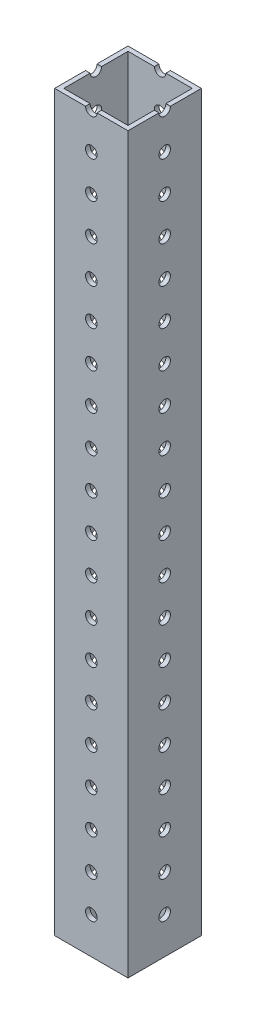
SolidWorks part; units mm, degrees
material "6061-T6 (SS)"
ref_plane "Front Plane" through (0, 0, 0) normal (0, 0, 1) x (1, 0, 0)
ref_plane "Top Plane" through (0, 0, 0) normal (0, 1, 0) x (1, 0, 0)
ref_plane "Right Plane" through (0, 0, 0) normal (1, 0, 0) x (0, 0, -1)
sketch "Sketch1" plane through (0, 0, 0) normal (0, 1, 0) x (1, 0, 0)
  line L0 (-11.1125, -11.1125) -> (-11.1125, 11.1125)
  line L1 (-12.7, -12.7) -> (12.7, -12.7)
  line L2 (-12.7, -12.7) -> (-12.7, 12.7)
  line L3 (-12.7, 12.7) -> (12.7, 12.7)
  line L4 (12.7, -12.7) -> (12.7, 12.7)
  line L5 (-12.7, -12.7) -> (12.7, 12.7) construction
  line L6 (-12.7, 12.7) -> (12.7, -12.7) construction
  line L7 (-11.1125, 11.1125) -> (11.1125, 11.1125)
  line L8 (11.1125, -11.1125) -> (11.1125, 11.1125)
  line L9 (-11.1125, -11.1125) -> (11.1125, -11.1125)
  point P0 (0, 0)
  dimension "D1" = 25.4
  dimension "D2" = 25.4
  dimension "D3" = 1.5875
extrude "Boss-Extrude1" add sketch "Sketch1" along normal blind 254
hole_wizard "#22 (0.157) Diameter Hole1" positions "Sketch2" profile "Sketch3" hole size "#22" standard "ANSI Inch" end condition through all
sketch "Sketch2" plane through (0, 0, 12.7) normal (0, 0, 1) x (1, 0, 0)
  line L0 (12.7, 254) -> (12.7, 0) construction
  line L1 (-12.7, 0) -> (12.7, 0) construction
  point P0 (0, 12.7)
  dimension "D1" = 12.7
  dimension "D2" = 12.7
sketch "Sketch3" plane through (0, 12.7, 12.7) normal (1, 0, 0) x (0, -1, 0)
  line L0 (0, 0) -> (0, 25.4)
  line L1 (0, 25.4) -> (1.9939, 25.4)
  line L2 (1.9939, 25.4) -> (1.9939, 0)
  line L5 (1.9939, 0) -> (0, 0)
  line L11 (0, -6.35) -> (0, 107.95) construction
  dimension "Thru Hole Dia." = 3.9878
  dimension "Thru Hole Depth" = 25.4
pattern_linear "LPattern1" count 20 spacing 12.7 along (0, 1, 0) of "#22 (0.157) Diameter Hole1"
hole_wizard "#22 (0.157) Diameter Hole2" positions "Sketch4" profile "Sketch5" hole size "#22" standard "ANSI Inch" end condition through all
sketch "Sketch4" plane through (12.7, 0, 0) normal (1, 0, 0) x (0, 0, -1)
  line L2 (-12.7, 254) -> (-12.7, 0) construction
  line L3 (-12.7, 0) -> (12.7, 0) construction
  point P0 (0, 12.7)
  dimension "D1" = 12.7
  dimension "D2" = 12.7
sketch "Sketch5" plane through (12.7, 12.7, 0) normal (0, 1, 0) x (0, 0, -1)
  line L0 (0, 0) -> (0, 25.4)
  line L1 (0, 25.4) -> (1.9939, 25.4)
  line L2 (1.9939, 25.4) -> (1.9939, 0)
  line L5 (1.9939, 0) -> (0, 0)
  line L11 (0, -6.35) -> (0, 107.95) construction
  dimension "Thru Hole Dia." = 3.9878
  dimension "Thru Hole Depth" = 25.4
pattern_linear "LPattern2" count 20 spacing 12.7 along (0, 1, 0) of "#22 (0.157) Diameter Hole2"
